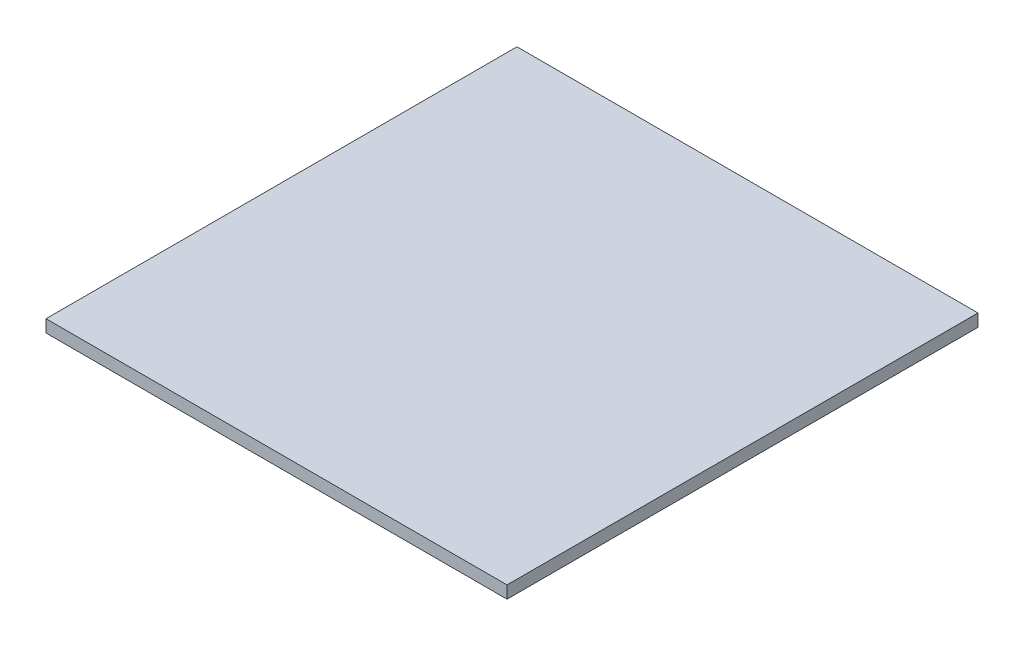
SolidWorks part; units mm, degrees
ref_plane "Front Plane" through (0, 0, 0) normal (0, 0, 1) x (1, 0, 0)
ref_plane "Top Plane" through (0, 0, 0) normal (0, 1, 0) x (1, 0, 0)
ref_plane "Right Plane" through (0, 0, 0) normal (1, 0, 0) x (0, 0, -1)
sketch "Sketch1" plane through (0, 0, 0) normal (0, 1, 0) x (1, 0, 0)
  line L1 (0, 0) -> (590.55, 0)
  line L2 (0, 0) -> (0, 603.25)
  line L3 (0, 603.25) -> (590.55, 603.25)
  line L4 (590.55, 0) -> (590.55, 603.25)
  dimension "D1" = 603.25
  dimension "D2" = 590.55
extrude "Boss-Extrude1" add sketch "Sketch1" along normal blind 15.875
